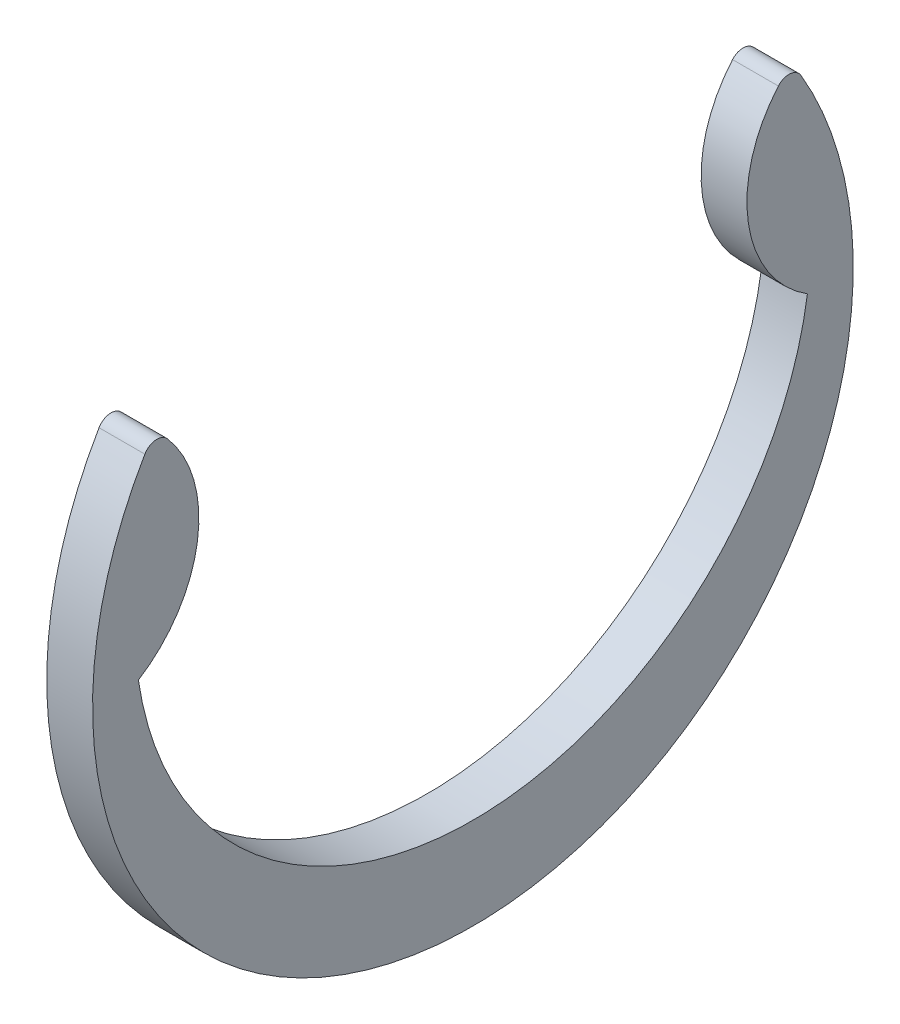
SolidWorks part; units mm, degrees
material "Cast Carbon Steel"
ref_plane "Front" through (0, 0, 0) normal (0, 0, 1) x (1, 0, 0)
ref_plane "Top" through (0, 0, 0) normal (0, 1, 0) x (1, 0, 0)
ref_plane "Right" through (0, 0, 0) normal (1, 0, 0) x (0, 0, -1)
sketch "Sketch1" plane through (0, 0, 0) normal (1, 0, 0) x (0, 0, -1)
  circle A0 centre (0, 0) radius 5.6007 construction
  arc A1 (-6.4897, 0) -> (6.4897, 0) centre (0, 0.9596) ccw
  circle A2 centre (0, 0) radius 7.3787 construction
  circle A3 centre (0, 0) radius 7.62 construction
  arc A4 (6.3643, 3.7338) -> (-6.3643, 3.7338) centre (0, 0) cw
  arc A5 (-5.9262, 3.7733) -> (-6.4897, 0) centre (-7.8362, 2.1298) cw
  arc A6 (-6.3643, 3.7338) -> (-5.9262, 3.7733) centre (-6.1311, 3.597) cw
  arc A7 (6.3643, 3.7338) -> (5.9262, 3.7733) centre (6.1311, 3.597) ccw
  arc A8 (6.4897, 0) -> (5.9262, 3.7733) centre (7.8362, 2.1298) cw
  arc A9 (5.9262, 3.7733) -> (6.4897, 0) centre (0, 0.9596) cw construction
  dimension "A" = 11.2014
  dimension "OD" = 14.7574
  dimension "D1" = 3.7338
  dimension "D2" = 12.9794
extrude "Extrude1" add sketch "Sketch1" along normal mid plane 0.889
sketch "Sketch2" plane through (0, 0, 0) normal (0, 0, 1) x (1, 0, 0)
  line L0 (-2.4765, 0) -> (7.4295, 0)
  line L1 (7.4295, 0) -> (7.4295, -6.35)
  line L3 (7.4295, -6.35) -> (0.4953, -6.35)
  line L4 (0.4953, -6.35) -> (0.4953, -5.715)
  line L5 (0.4953, -5.715) -> (-0.4953, -5.715)
  line L6 (-0.4953, -5.715) -> (-0.4953, -6.35)
  line L7 (-0.4953, -6.35) -> (-2.4765, -6.35) construction
  line L8 (-2.4765, -6.35) -> (-2.4765, 0) construction
  line L9 (0, -5.715) -> (0, 0) construction
  line L10 (7.4295, 0) -> (14.0551, 0) construction
  line L11 (-0.4953, -6.35) -> (-2.159, -6.35)
  line L12 (-2.159, -6.35) -> (-2.4765, -6.0325)
  line L13 (-2.4765, -6.0325) -> (-2.4765, 0)
  point P14 (-0.4953, -6.0325)
  dimension "D2" = 9.906
  dimension "D3" = 2.4765
  dimension "D4" = 45
revolve "Revolve1" [suppressed] add sketch "Sketch2" angle 360 about L10
equation "\"D2@Sketch2\" = \"W@Sketch2\"*10"
equation "\"D3@Sketch2\" = \"D2@Sketch2\"/4"
equation "\"D1@Sketch1\" = \"A@Sketch1\"/3"
equation "\"D2@Sketch1\" = (\"OD@Sketch1\"+\"A@Sketch1\")/2"
